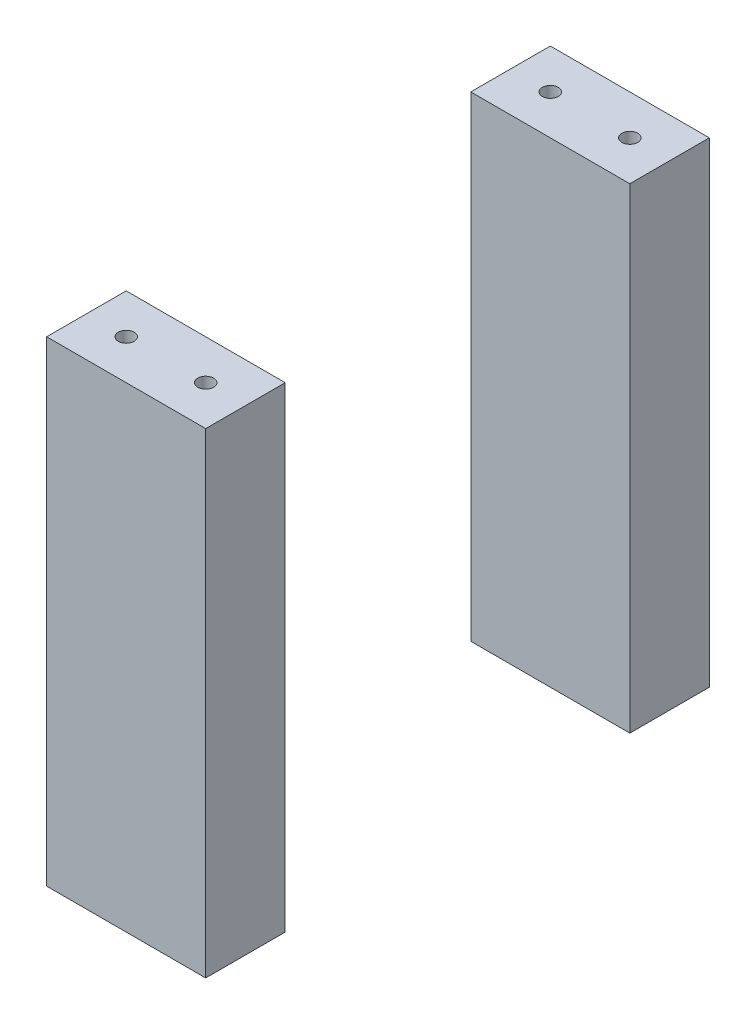
SolidWorks part; units mm, degrees
ref_plane "Ebene vorne" through (0, 0, 0) normal (0, 0, 1) x (1, 0, 0)
ref_plane "Ebene oben" through (0, 0, 0) normal (0, 1, 0) x (1, 0, 0)
ref_plane "Ebene rechts" through (0, 0, 0) normal (1, 0, 0) x (0, 0, -1)
sketch "OutlineBase" plane through (0, 0, 0) normal (0, 1, 0) x (1, 0, 0)
  line L0 (0, -95) -> (0, -285) construction
  line L1 (55, -285) -> (55, -95)
  line L2 (55, -285) -> (-55, -285)
  line L3 (-55, -285) -> (-55, -95)
  line L4 (55, -95) -> (-55, -95)
  line L5 (55, -285) -> (-55, -95) construction
  line L6 (-55, -285) -> (55, -95) construction
  line L16 (0, -190) -> (0, -150.9424) construction
  line L27 (-30, -285) -> (-30, -255)
  line L28 (-30, -285) -> (30, -285)
  line L29 (30, -285) -> (30, -255)
  line L30 (-30, -255) -> (30, -255)
  line L31 (0, -255) -> (-30, -255)
  line L32 (30, -255) -> (-30, -255)
  line L34 (30, -285) -> (-30, -285)
  line L35 (0, -190) -> (89.9295, -190) construction
  line L36 (30, -95) -> (-30, -95)
  line L39 (0, -125) -> (-30, -125)
  line L40 (-30, -125) -> (30, -125)
  line L41 (30, -95) -> (30, -125)
  line L42 (-30, -95) -> (30, -95)
  line L43 (-30, -95) -> (-30, -125)
  circle A0 centre (-15, -270) radius 3
  circle A1 centre (15, -270) radius 3
  circle A4 centre (15, -270) radius 3
  circle A5 centre (-15, -270) radius 3
  circle A6 centre (-15, -110) radius 3
  circle A7 centre (15, -110) radius 3
  circle A8 centre (15, -110) radius 3
  circle A9 centre (-15, -110) radius 3
  point P33 (0, -190)
sketch "GroundHeight" plane through (0, 0, 0) normal (0, 0, 1) x (1, 0, 0)
  line L1 (-150, -16) -> (150, -16)
  line L2 (-150, -16) -> (-150, -21)
  line L3 (-150, -21) -> (150, -21)
  line L4 (150, -16) -> (150, -21)
sketch "BaseWormGearHeight" plane through (0, 0, 0) normal (1, 0, 0) x (0, 0, -1)
  line L1 (-95, 169.5) -> (-285, 169.5)
  line L2 (-95, 169.5) -> (-95, 163.5)
  line L3 (-95, 163.5) -> (-285, 163.5)
  line L4 (-285, 169.5) -> (-285, 163.5)
  line L5 (-190, 169.5) -> (-190, 212) construction
  line L6 (0, 218) -> (0, 227) construction
  line L8 (-190, 212) -> (-190, 217) construction
  line L9 (-190, 217) -> (-190, 227) construction
  point P4 (-190, 163.5)
sketch "Skizze4" plane through (0, 0, 0) normal (0, 1, 0) x (1, 0, 0)
  line L1 (-30, -95) -> (30, -95)
  line L2 (-30, -95) -> (-30, -125)
  line L3 (-30, -125) -> (30, -125)
  line L4 (30, -95) -> (30, -125)
  line L5 (-30, -255) -> (30, -255)
  line L6 (-30, -255) -> (-30, -285)
  line L7 (-30, -285) -> (30, -285)
  line L8 (30, -255) -> (30, -285)
  circle A0 centre (-15, -110) radius 3
  circle A1 centre (15, -110) radius 3
  circle A2 centre (15, -270) radius 3
  circle A3 centre (-15, -270) radius 3
sketch "Skizze5" plane through (0, 0, 0) normal (1, 0, 0) x (0, 0, -1)
  point P0 (-95, 163.5)
extrude "Aufsatz-Linear austragen1" add sketch "Skizze4" along normal up to vertex (163.5 mm away) and the other way up to vertex (16 mm away) up to point (0, 163.5, 95) other way up to point (150, -16, 0)
